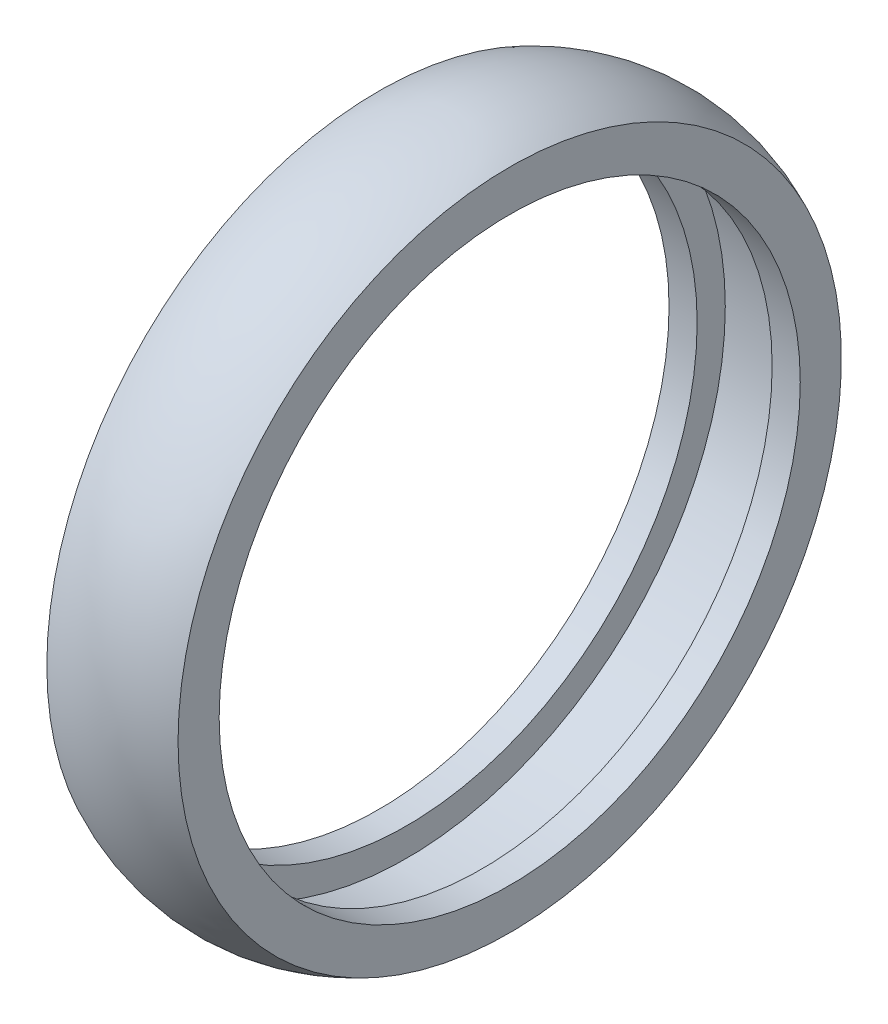
SolidWorks part; units mm, degrees
ref_plane "Front Plane" through (0, 0, 0) normal (0, 0, 1) x (1, 0, 0)
ref_plane "Top Plane" through (0, 0, 0) normal (0, 1, 0) x (1, 0, 0)
ref_plane "Right Plane" through (0, 0, 0) normal (1, 0, 0) x (0, 0, -1)
sketch "Sketch1" plane through (0, 0, 0) normal (0, 0, 1) x (1, 0, 0)
  line L0 (-690.4668, 0) -> (33832.8751, 0) construction
  line L1 (0, -690.4668) -> (0, 33832.8751) construction
  line L2 (4, 34) -> (-4, 34)
  line L3 (-4, 34) -> (-4, 31)
  line L4 (-4, 31) -> (-7, 31)
  line L5 (-7, 31) -> (-7, 35.3875)
  line L7 (7, 31) -> (7, 35.3875)
  line L8 (4, 31) -> (7, 31)
  line L9 (4, 34) -> (4, 31)
  arc A0 (-7, 35.3875) -> (7, 35.3875) centre (0, 21) cw
  dimension "D6" = 16
  dimension "D1" = 68
  dimension "D3" = 3
  dimension "D4" = 8
  dimension "D5" = 3
  dimension "D2" = 3
revolve "Revolve1" add sketch "Sketch1" angle 360 about L0
equation "\"width\"= 24"
equation "\"thk\"= 3"
equation "\"holesize\"= 4.2"
equation "\"holedistance\"= ( 20 + 12 ) / 2"
equation "\"threaded_hole\"= 3.9"
equation "\"fillet_radius\"= 2"
equation "\"ground_clearance\"= 25"
equation "\"tire_thk\"= 3"
equation "\"innerwheel_diam\" = \"wheel_diam\"-2*\"tire_thk\""
equation "\"innerwheel_thk\"= 8"
equation "\"wheel_diam\"= 2*(\"width\"/2+\"ground_clearance\")"
equation "\"D1@Sketch1\"=\"innerwheel_diam\""
equation "\"D3@Sketch1\"=\"D2@Sketch1\""
equation "\"D4@Sketch1\"=\"innerwheel_thk\""
equation "\"D2@Sketch1\"=\"tire_thk\""
